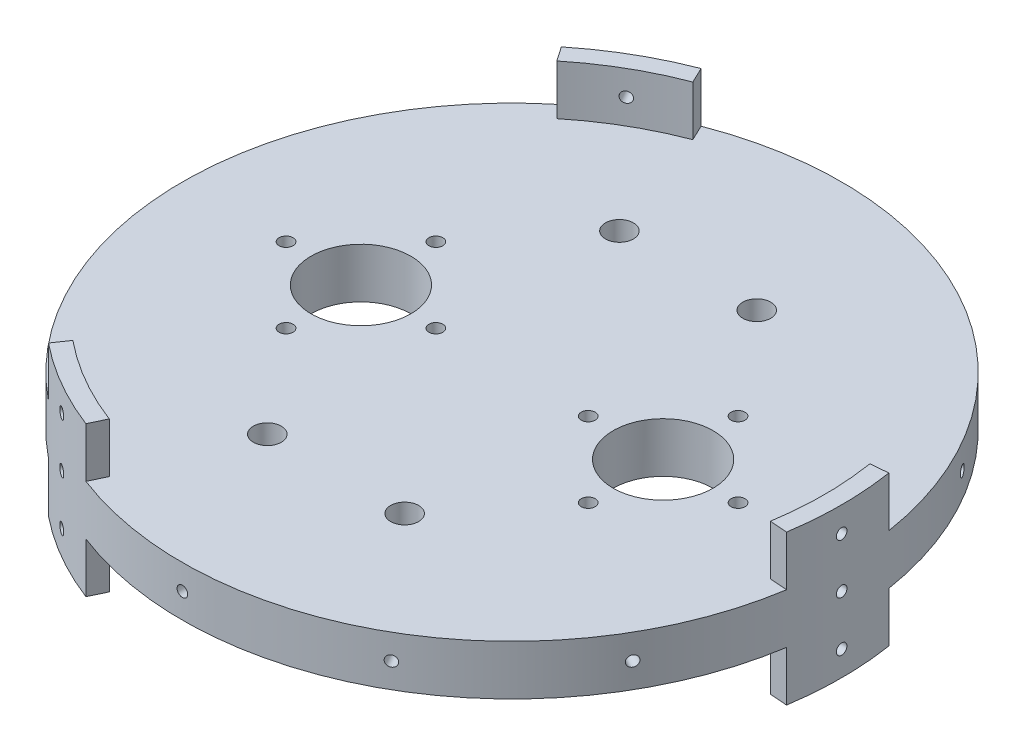
SolidWorks part; units mm, degrees
material "6061-T6 (SS)"
ref_plane "Front" through (0, 0, 0) normal (0, 0, 1) x (1, 0, 0)
ref_plane "Top" through (0, 0, 0) normal (0, 1, 0) x (1, 0, 0)
ref_plane "Right" through (0, 0, 0) normal (1, 0, 0) x (0, 0, -1)
sketch "Sketch1" plane through (0, 0, 0) normal (0, 1, 0) x (1, 0, 0)
  line L1 (0, 0) -> (127.635, 0)
  line L2 (0, 0) -> (0, 127.635)
  line L3 (0, 127.635) -> (127.635, 127.635)
  line L4 (127.635, 0) -> (127.635, 127.635)
  dimension "D1" = 127.635
  dimension "D2" = 127.635
extrude "Main Plate" add sketch "Sketch1" along normal blind 12.7
sketch "Sketch9" plane through (0, 12.7, 0) normal (0, 1, 0) x (1, 0, 0)
  circle A0 centre (63.8175, 63.8175) radius 85.725
  dimension "D1" = 171.45
extrude "Boss-Extrude1" add sketch "Sketch9" against normal up to surface (12.7 mm away) contours A0 up to face at (63.8175, 0, -63.8175)
sketch "Sketch10" plane through (0, 12.7, 0) normal (0, 1, 0) x (1, 0, 0)
  circle A0 centre (63.8175, 63.8175) radius 97.0396
  circle A1 centre (63.8175, 63.8175) radius 83.82
extrude "Cut-Extrude1" cut sketch "Sketch10" against normal blind 167.64 contours A0 | A1
sketch "Sketch14" plane through (0, 12.7, 0) normal (0, 1, 0) x (1, 0, 0)
  line L0 (201.1692, 63.8175) -> (-73.4523, 63.8175) construction
ref_plane "Plane1" through (0, 0, -63.8175) normal (0, 0, -1) x (-1, 0, 0)
ref_plane "Plane3" through (0, 6.35, 0) normal (0, 1, 0) x (1, 0, 0)
ref_plane "Plane2" through (-20.0025, 0, 0) normal (-1, 0, 0) x (0, 0, 1)
sketch "Sketch18" plane through (0, 6.35, 0) normal (0, 1, 0) x (1, 0, 0)
  circle A0 centre (63.8175, 63.8175) radius 83.82
  circle A1 centre (63.8175, 63.8175) radius 79.375
  dimension "D1" = 158.75
extrude "Boss-Extrude2" add sketch "Sketch18" along normal mid plane 38.1
sketch "Sketch15" plane through (-20.0025, 0, 0) normal (-1, 0, 0) x (0, 0, 1)
  line L0 (-63.8175, 87.3125) -> (-63.8175, -87.3125) construction
  line L1 (20.0025, 12.7) -> (-147.6375, 12.7) construction
  line L2 (-147.6375, -12.7) -> (20.0025, -12.7) construction
  line L3 (15.5575, 25.4) -> (-143.1925, 25.4) construction
  circle A0 centre (-63.8175, 6.35) radius 1.3526
  circle A1 centre (-63.8175, 19.05) radius 1.3525
  circle A2 centre (-63.8175, -6.35) radius 1.3526
  dimension "D1" = 2.7051
  dimension "D2" = 6.35
  dimension "D3" = 2.7051
  dimension "D4" = 2.7051
  dimension "D5" = 6.35
  dimension "D6" = 6.35
extrude "Cut-Extrude3" cut sketch "Sketch15" against normal blind 15.24
pattern_circular "CirPattern1" count 12 over 360 about axis through (63.8175, 0, -63.8175) along (0, 1, 0) of "Cut-Extrude3"
sketch "Sketch20" plane through (0, 12.7, 0) normal (0, 1, 0) x (1, 0, 0)
  line L0 (63.8175, 143.1925) -> (63.8175, -15.5575) construction
  line L1 (-15.5575, 63.8175) -> (143.1925, 63.8175) construction
  circle A0 centre (63.8175, 63.8175) radius 79.375 construction
ref_plane "Plane4" through (63.8175, 0, 0) normal (-1, 0, 0) x (0, 0, 1)
sketch "Sketch21" plane through (0, 12.7, 0) normal (0, 1, 0) x (1, 0, 0)
  line L1 (-15.5575, 63.8175) -> (143.1925, 63.8175) construction
  line L2 (102.235, 63.8175) -> (102.235, 100.651) construction
  line L3 (63.8175, 87.3125) -> (63.8175, -87.3125) construction
  circle A0 centre (102.235, 63.8175) radius 12.7
  circle A1 centre (102.235, 82.8675) radius 1.778
  circle A2 centre (25.4, 63.8175) radius 12.7
  circle A3 centre (121.285, 63.8175) radius 1.778
  circle A4 centre (102.235, 44.7675) radius 1.778
  circle A5 centre (83.185, 63.8175) radius 1.778
  circle A6 centre (25.4, 82.8675) radius 1.778
  circle A7 centre (6.35, 63.8175) radius 1.778
  circle A8 centre (25.4, 44.7675) radius 1.778
  circle A9 centre (44.45, 63.8175) radius 1.778
  dimension "D1" = 25.4
  dimension "D2" = 3.556
  dimension "D6" = 19.05
  dimension "D3" = 19.05
  dimension "D4" = 76.835
  dimension "D7" = 19.05
  dimension "D5" = 4
extrude "CO2 Mounts" cut sketch "Sketch21" against normal through all
sketch "Sketch22" plane through (0, 12.7, 0) normal (0, 1, 0) x (1, 0, 0)
  line L0 (63.8175, 87.3125) -> (63.8175, -87.3125) construction
  line L1 (87.3125, 63.8175) -> (-87.3125, 63.8175) construction
  circle A0 centre (46.355, 108.585) radius 3.556
  circle A1 centre (81.28, 108.585) radius 3.556
  circle A2 centre (81.28, 19.05) radius 3.556
  circle A3 centre (46.355, 19.05) radius 3.556
  dimension "D1" = 7.112
  dimension "D2" = 34.925
  dimension "D3" = 89.535
extrude "Cut-Extrude5" cut sketch "Sketch22" against normal through all
sketch "Sketch23" plane through (0, 12.7, 0) normal (0, 1, 0) x (1, 0, 0)
  line L0 (13.6787, 125.352) -> (7.5523, 134.2379)
  line L1 (15.1867, 11.8815) -> (13.6787, 2.283) construction
  line L3 (-15.5575, 63.8175) -> (143.1925, 63.8175) construction
  line L4 (63.8175, 143.1925) -> (63.8175, -15.5575) construction
  line L5 (-15.5575, 63.8175) -> (143.1925, 63.8175)
  line L6 (63.8175, 143.1925) -> (63.8175, -15.5575)
  line L7 (13.6787, 2.283) -> (6.9592, -7.4631)
  line L8 (-19.2671, 125.3206) -> (-48.797, 60.3978)
  line L9 (-48.797, 60.3978) -> (-9.8843, 7.0525)
  line L10 (-9.8843, 7.0525) -> (6.9592, -7.4631)
  line L11 (24.1345, -4.9259) -> (13.6787, 2.283) construction
  line L14 (7.5523, 134.2379) -> (-19.2671, 125.3206)
  line L15 (24.1345, 132.5609) -> (13.6787, 125.352) construction
  line L28 (63.8175, 63.8175) -> (24.1345, -4.9259) construction
  line L29 (63.8175, 63.8175) -> (24.1345, 132.5609) construction
  line L30 (142.1773, 76.4717) -> (152.9359, 77.3344)
  line L31 (152.9359, 77.3344) -> (158.6231, 105.0193)
  line L32 (158.6231, 105.0193) -> (117.1632, 163.0543)
  line L33 (117.1632, 163.0543) -> (51.5085, 156.0277)
  line L34 (51.5085, 156.0277) -> (30.5159, 148.6985)
  line L35 (35.5964, 138.0062) -> (30.5159, 148.6985)
  line L36 (35.5964, -10.3712) -> (30.9643, -20.1198)
  line L37 (30.9643, -20.1198) -> (52.0965, -38.8874)
  line L38 (52.0965, -38.8874) -> (123.0863, -31.9996)
  line L39 (123.0863, -31.9996) -> (149.8284, 28.3723)
  line L40 (149.8284, 28.3723) -> (153.9775, 50.217)
  line L41 (142.1773, 51.1633) -> (153.9775, 50.217)
  circle A0 centre (63.8175, 63.8175) radius 79.375 construction
  arc A1 (13.6787, 2.283) -> (13.6787, 125.352) centre (63.8175, 63.8175) cw
  circle A3 centre (63.8175, 63.8175) radius 79.375
  circle A4 centre (63.8175, 63.8175) radius 79.375
  arc A6 (35.5964, 138.0062) -> (142.1773, 76.4717) centre (63.8175, 63.8175) cw
  arc A7 (142.1773, 51.1633) -> (35.5964, -10.3712) centre (63.8175, 63.8175) cw
  dimension "D1" = 79.375
  dimension "D2" = 0
  dimension "D3" = 12.7
  dimension "D4" = 90
  dimension "D5" = 12.7
  dimension "D6" = 90
  dimension "D8" = 60.004
  dimension "D9" = 60.004
  dimension "D7" = 3
extrude "Cut-Extrude6" cut sketch "Sketch23" along normal up to next (12.7 mm away)
mirror "Mirror1" about plane through (0, 6.35, 0) normal (0, 1, 0) of "Cut-Extrude6"
sketch "Sketch25" plane through (0, 0, 0) normal (0, -1, 0) x (1, 0, 0)
  line L0 (-15.5575, -63.8175) -> (143.1925, -63.8175) construction
  line L1 (63.8175, -143.1925) -> (63.8175, 15.5575) construction
  line L2 (-15.5575, -63.8175) -> (143.1925, -63.8175)
  line L3 (63.8175, -143.1925) -> (63.8175, 15.5575)
  circle A0 centre (46.355, -19.05) radius 6.35
  circle A1 centre (81.28, -19.05) radius 6.35
  circle A2 centre (81.28, -108.585) radius 6.35
  circle A3 centre (46.355, -108.585) radius 6.35
  dimension "D1" = 12.7
